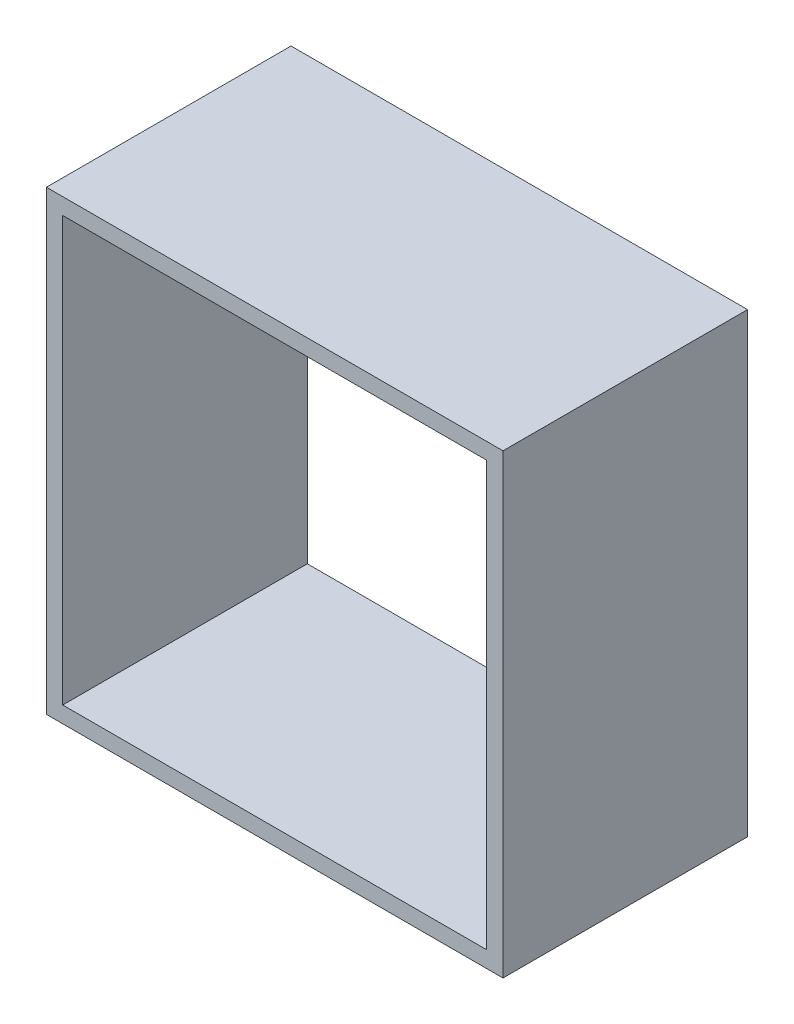
SolidWorks part; units mm, degrees
ref_plane "Front Plane" through (0, 0, 0) normal (0, 0, 1) x (1, 0, 0)
ref_plane "Top Plane" through (0, 0, 0) normal (0, 1, 0) x (1, 0, 0)
ref_plane "Right Plane" through (0, 0, 0) normal (1, 0, 0) x (0, 0, -1)
sketch "Sketch1" plane through (0, 0, 0) normal (0, 0, 1) x (1, 0, 0)
  line L0 (14, 14) -> (-14, 14)
  line L1 (13, -13) -> (-13, -13)
  line L2 (13, -13) -> (13, 13)
  line L3 (13, 13) -> (-13, 13)
  line L4 (-13, -13) -> (-13, 13)
  line L5 (13, -13) -> (-13, 13) construction
  line L6 (13, 13) -> (-13, -13) construction
  line L7 (-14, -14) -> (-14, 14)
  line L8 (14, -14) -> (-14, -14)
  line L9 (14, -14) -> (14, 14)
  point P0 (0, 0)
  dimension "D1" = 26
  dimension "D2" = 1
extrude "Boss-Extrude1" add sketch "Sketch1" along normal blind 15
